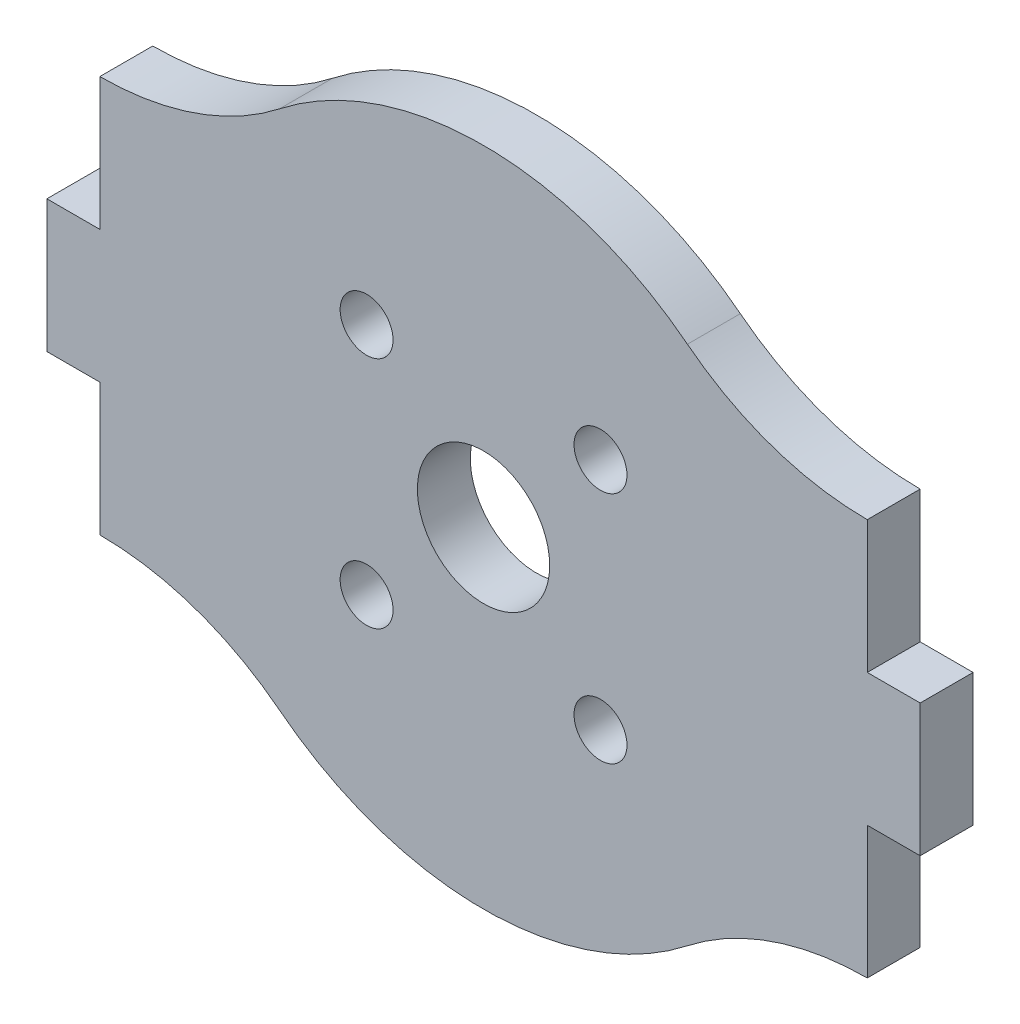
SolidWorks part; units mm, degrees
material "3.1325 (EN-AW 2017A)"
ref_plane "Plan de face" through (0, 0, 0) normal (0, 0, 1) x (1, 0, 0)
ref_plane "Plan de dessus" through (0, 0, 0) normal (0, 1, 0) x (1, 0, 0)
ref_plane "Plan de droite" through (0, 0, 0) normal (1, 0, 0) x (0, 0, -1)
sketch "Esquisse1" plane through (0, 0, 0) normal (0, 0, 1) x (1, 0, 0)
  line L0 (33, -5) -> (33, 5)
  line L1 (33, 0) -> (0, 0) construction
  line L2 (33, 5) -> (29, 5)
  line L3 (29, 5) -> (29, 15)
  line L4 (29, 15) -> (-20.4023, 15) construction
  line L5 (0, 0) -> (0, 26) construction
  line L6 (-33, -5) -> (-33, 5)
  line L7 (-33, 5) -> (-29, 5)
  line L8 (-29, 5) -> (-29, 15)
  line L9 (-33, -5) -> (-29, -5)
  line L10 (-29, -5) -> (-29, -15)
  line L11 (29, -5) -> (29, -15)
  line L12 (33, -5) -> (29, -5)
  line L14 (-8.8388, -8.8388) -> (8.8388, -8.8388) construction
  line L15 (-8.8388, -8.8388) -> (-8.8388, 8.8388) construction
  line L16 (-8.8388, 8.8388) -> (8.8388, 8.8388) construction
  line L17 (8.8388, -8.8388) -> (8.8388, 8.8388) construction
  line L18 (-8.8388, -8.8388) -> (8.8388, 8.8388) construction
  line L19 (-8.8388, 8.8388) -> (8.8388, -8.8388) construction
  circle A0 centre (0, 0) radius 5
  circle A1 centre (-8.8388, 8.8388) radius 2
  circle A2 centre (8.8388, 8.8388) radius 2
  circle A3 centre (8.8388, -8.8388) radius 2
  circle A4 centre (-8.8388, -8.8388) radius 2
  arc A5 (15.4091, 19.6865) -> (-15.4091, 19.6865) centre (0, 0) ccw
  arc A6 (29, 15) -> (15.4091, 19.6865) centre (29, 37.05) cw
  arc A7 (-29, 15) -> (-15.4091, 19.6865) centre (-29, 37.05) ccw
  arc A8 (-29, -15) -> (-15.4091, -19.6865) centre (-29, -37.05) cw
  arc A9 (15.4091, -19.6865) -> (-15.4091, -19.6865) centre (0, 0) cw
  arc A10 (29, -15) -> (15.4091, -19.6865) centre (29, -37.05) ccw
  point P14 (0, 0)
  point P27 (-33, 0)
  dimension "D1" = 10
  dimension "D3" = 4
  dimension "D9" = 25
  dimension "D2" = 25
  dimension "D5" = 5
  dimension "D6" = 33
  dimension "D7" = 4
  dimension "D8" = 10
  dimension "D4" = 4
extrude "Boss.-Extru.1" add sketch "Esquisse1" along normal blind 4
